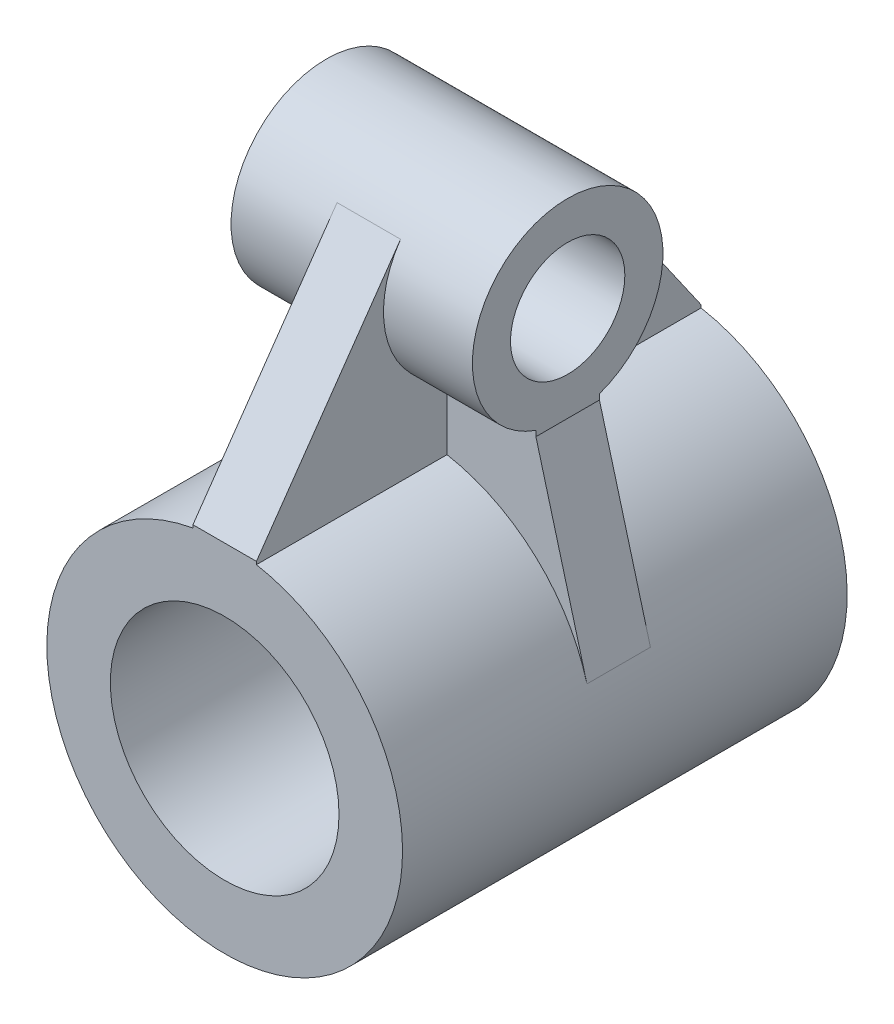
SolidWorks part; units mm, degrees
material "1060 Alloy"
ref_plane "Front Plane" through (0, 0, 0) normal (0, 0, 1) x (1, 0, 0)
ref_plane "Top Plane" through (0, 0, 0) normal (0, 1, 0) x (1, 0, 0)
ref_plane "Right Plane" through (0, 0, 0) normal (1, 0, 0) x (0, 0, -1)
sketch "Sketch1" plane through (0, 0, 0) normal (0, 0, 1) x (1, 0, 0)
  circle A0 centre (0, 0) radius 9
  circle A1 centre (0, 0) radius 14
  dimension "D1" = 28
  dimension "D2" = 18
extrude "Boss-Extrude1" add sketch "Sketch1" along normal mid plane 35
sketch "Sketch7" plane through (0, 0, 0) normal (1, 0, 0) x (0, 0, -1)
  circle A0 centre (0, 26) radius 4.5
  circle A1 centre (0, 26) radius 7.5
  dimension "D2" = 15
  dimension "D3" = 9
  dimension "D1" = 26
extrude "Boss-Extrude5" add sketch "Sketch7" along normal mid plane 19 separate body
sketch "Sketch8" plane through (0, 0, 0) normal (1, 0, 0) x (0, 0, -1)
  line L0 (-17.5, 14) -> (-6.154, 30.287)
  line L1 (17.5, 14) -> (6.154, 30.287)
  line L4 (17.5, 14) -> (17.5, 9)
  line L5 (17.5, 9) -> (-17.5, 9)
  line L6 (-17.5, 9) -> (-17.5, 14)
  circle A0 centre (0, 26) radius 7.5 construction
  arc A1 (-6.154, 30.287) -> (6.154, 30.287) centre (0, 26) ccw
extrude "Boss-Extrude7" add sketch "Sketch8" along normal mid plane 5
sketch "Sketch9" plane through (0, 0, 0) normal (0, 0, 1) x (1, 0, 0)
  line L2 (9.5, 18.5) -> (9.5, 21.5)
  line L4 (9.5, 21.5) -> (-9.5, 21.5)
  line L5 (-9.5, 21.5) -> (-9.5, 18.5)
  line L6 (-9.5, 18.5) -> (-13.5146, 3.6547)
  line L7 (9.5, 18.5) -> (13.5146, 3.6547)
  circle A0 centre (0, 0) radius 14 construction
  arc A1 (13.5146, 3.6547) -> (-13.5146, 3.6547) centre (0, 0) ccw
extrude "Boss-Extrude8" add sketch "Sketch9" along normal mid plane 5
